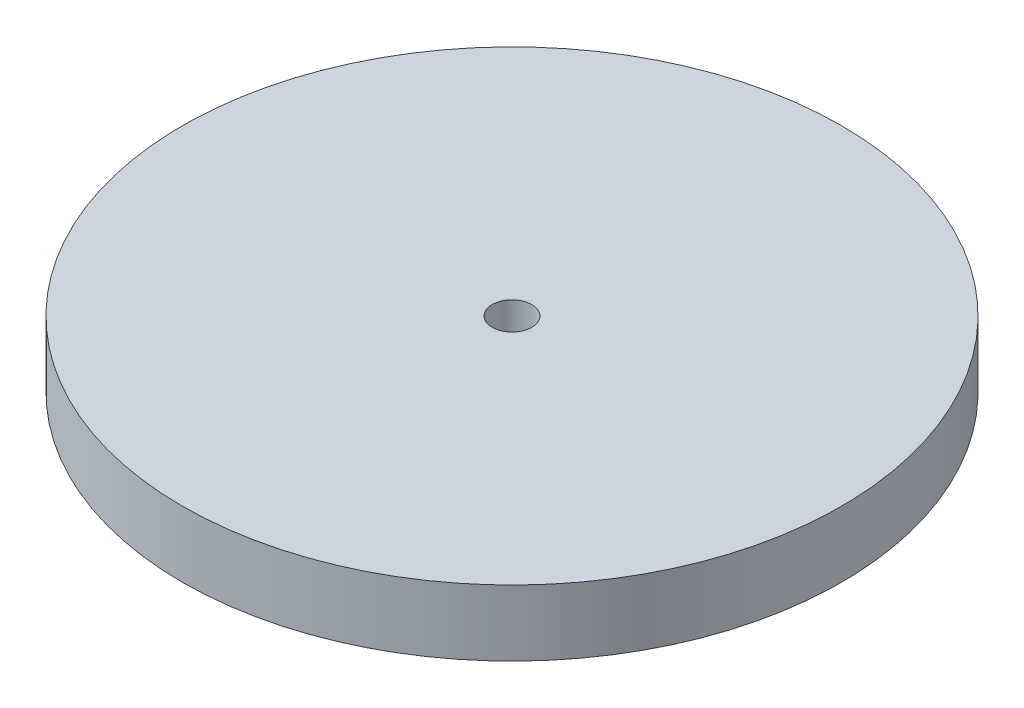
SolidWorks part; units mm, degrees
ref_plane "Front Plane" through (0, 0, 0) normal (0, 0, 1) x (1, 0, 0)
ref_plane "Top Plane" through (0, 0, 0) normal (0, 1, 0) x (1, 0, 0)
ref_plane "Right Plane" through (0, 0, 0) normal (1, 0, 0) x (0, 0, -1)
sketch "Sketch1" plane through (0, 0, 0) normal (0, 1, 0) x (1, 0, 0)
  circle A0 centre (0, 0) radius 3
  circle A1 centre (0, 0) radius 50
  dimension "D1" = 100
  dimension "D2" = 6
extrude "Boss-Extrude1" add sketch "Sketch1" along normal blind 10
